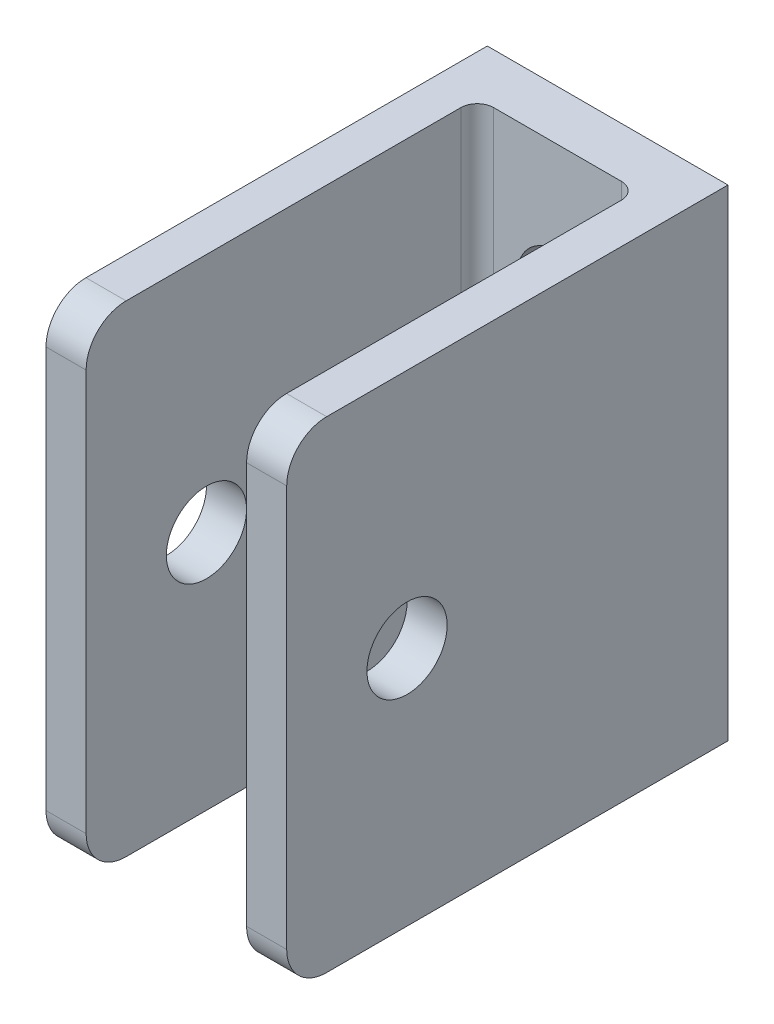
SolidWorks part; units mm, degrees
ref_plane "Front" through (0, 0, 0) normal (0, 0, 1) x (1, 0, 0)
ref_plane "Top" through (0, 0, 0) normal (0, 1, 0) x (1, 0, 0)
ref_plane "Right" through (0, 0, 0) normal (1, 0, 0) x (0, 0, -1)
sketch "Sketch1" plane through (0, 0, 0) normal (0, 1, 0) x (1, 0, 0)
  line L0 (-9.525, 0) -> (9.525, 0)
  line L3 (9.525, 0) -> (9.525, -34.925)
  line L4 (9.525, -34.925) -> (6.35, -34.925)
  line L5 (6.35, -34.925) -> (6.35, -3.9688)
  line L6 (6.35, -3.9688) -> (-6.35, -3.9688)
  line L7 (-6.35, -3.9688) -> (-6.35, -34.925)
  line L8 (-6.35, -34.925) -> (-9.525, -34.925)
  line L9 (-9.525, -34.925) -> (-9.525, 0)
  line L12 (0, -3.9688) -> (0, 0) construction
extrude "Extrude1" add sketch "Sketch1" along normal mid plane 38.1
sketch "Sketch2" plane through (0, 0, 0) normal (0, 0, 1) x (1, 0, 0)
  line L0 (-1.27, 0) -> (1.27, 0) construction
  line L2 (0, 8.5725) -> (0, -8.5725) construction
  circle A0 centre (0, -8.5725) radius 3.175
  circle A1 centre (0, 8.5725) radius 3.175
extrude "Extrude2" cut sketch "Sketch2" along normal through all
other "DeleteFace1" [suppressed]
pattern_linear "LPattern1" [suppressed] count 2 spacing 1.27 count 2 spacing 1.27
other "DeleteFace2" [suppressed]
other "DeleteFace3" [suppressed]
sketch "Sketch5" [suppressed] plane through (0, 0, 10.3188) normal (0, 0, 1) x (1, 0, 0)
  circle A0 centre (-9.525, -6.35) radius 5.08
  circle A1 centre (9.525, 6.35) radius 5.08
  dimension "D1" = 10.16
extrude "Cut-Extrude1" [suppressed] cut sketch "Sketch5" against normal blind 1.9844
sketch "Sketch3" plane through (0, 0, -0.6698) normal (1, 0, 0) x (0, 0, -1)
  line L1 (-35.5948, 19.05) -> (-35.5948, -19.05) construction
  circle A0 centre (-26.0698, 0) radius 3.175
  dimension "D1" = 6.35
extrude "Extrude3" cut sketch "Sketch3" along normal through all and the other way through all
fillet "Fillet3" radius 3.1623 4 edges at (7.9375, -19.05, 34.925) (7.9375, 19.05, 34.925) (-7.9375, -19.05, 34.925) (-7.9375, 19.05, 34.925)
sketch "Sketch4" plane through (0, 0, 0) normal (0, 1, 0) x (1, 0, 0)
  line L0 (9.525, -22.225) -> (6.35, -22.225) construction
  line L1 (6.35, -28.575) -> (9.525, -28.575) construction
  line L2 (-6.35, -22.225) -> (-9.525, -22.225) construction
  line L3 (-9.525, -28.575) -> (-6.35, -28.575) construction
  line L4 (9.525, -22.225) -> (6.35, -22.225)
  line L5 (6.35, -28.575) -> (9.525, -28.575)
  line L6 (-6.35, -22.225) -> (-9.525, -22.225)
  line L7 (-9.525, -28.575) -> (-6.35, -28.575)
  line L8 (-10.541, -25.4) -> (-5.334, -25.4) construction
  line L9 (-6.35, -25.4) -> (-9.525, -25.4) construction
  line L10 (5.334, -25.4) -> (10.541, -25.4) construction
  point P14 (-7.9375, -25.4)
  point P15 (-7.9375, -22.225)
  point P16 (7.9375, -25.4)
  point P17 (7.9375, -22.225)
  dimension "D1" = 1.016
fillet "Fillet4" radius 1.3017 2 edges at (6.35, 0, 3.9688) (-6.35, 0, 3.9688)
equation "\"D1@Sketch3\" = \"Hole Dia@Sketch2\""
equation "\"D1@Fillet3\" = \"B@Extrude1\" * .083"
equation "\"D1@Fillet4\" = \"Wall Thickness 1@Sketch1\" * .41"
equation "\"D3@LPattern1\" = \"Hole Spacing 3@Sketch2\" * .5"
equation "\"D4@LPattern1\" = \"Hole Spacing 3@Sketch2\" * .5"
equation "\"D1@Sketch5\" = \"Hole Dia@Sketch2\" * 1.6"
equation "\"D1@Cut-Extrude1\" = \"Wall Thickness 2@Sketch1\" * .5"
